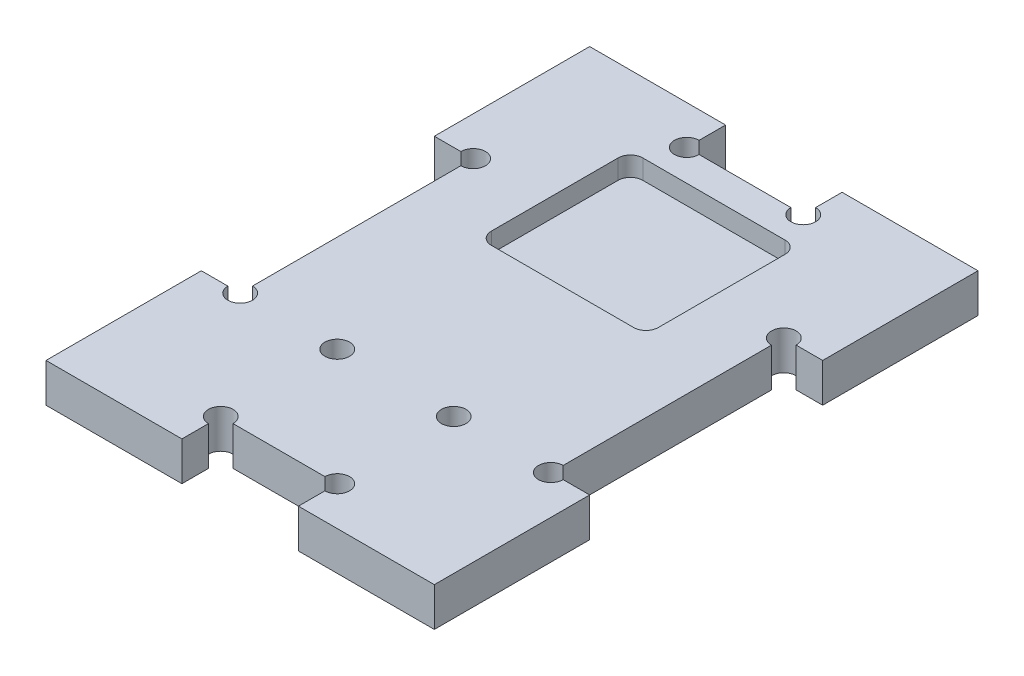
SolidWorks part; units mm, degrees
material "Acrylic (Medium-high impact)"
ref_plane "Front Plane" through (0, 0, 0) normal (0, 0, 1) x (1, 0, 0)
ref_plane "Top Plane" through (0, 0, 0) normal (0, 1, 0) x (1, 0, 0)
ref_plane "Right Plane" through (0, 0, 0) normal (1, 0, 0) x (0, 0, -1)
sketch "Sketch1" plane through (0, 0, 0) normal (0, 1, 0) x (1, 0, 0)
  line L1 (0, 0) -> (50, 0)
  line L2 (0, 0) -> (0, 70)
  line L3 (0, 70) -> (50, 70)
  line L4 (50, 0) -> (50, 70)
  dimension "D1" = 70
  dimension "D2" = 50
extrude "Boss-Extrude1" add sketch "Sketch1" along normal blind 5
sketch "Sketch4" plane through (0, 0, 0) normal (0, -1, 0) x (1, 0, 0)
  line L0 (25, 0) -> (25, -70) construction
  line L1 (34.1625, -61) -> (15.8375, -61)
  line L2 (35.75, -59.4125) -> (35.75, -43.0875)
  line L3 (34.1625, -41.5) -> (15.8375, -41.5)
  line L4 (14.25, -59.4125) -> (14.25, -43.0875)
  line L5 (35.75, -61) -> (14.25, -41.5) construction
  line L6 (35.75, -41.5) -> (14.25, -61) construction
  line L7 (50, -70) -> (0, -70) construction
  line L8 (0, 0) -> (50, 0) construction
  arc A0 (15.8375, -61) -> (14.25, -59.4125) centre (15.8375, -59.4125) cw
  arc A1 (34.1625, -61) -> (35.75, -59.4125) centre (34.1625, -59.4125) ccw
  arc A2 (35.75, -43.0875) -> (34.1625, -41.5) centre (34.1625, -43.0875) ccw
  arc A3 (15.8375, -41.5) -> (14.25, -43.0875) centre (15.8375, -43.0875) ccw
  point P0 (25, -51.25)
  dimension "D3" = 1.5875
  dimension "D1" = 19.5
  dimension "D2" = 21.5
  dimension "D4" = 9
extrude "Cut-Extrude2" cut sketch "Sketch4" along direction (0, -1, 0) on the side against the normal blind 2.5 from offset 2.5 offset against normal yes
sketch "Sketch5" plane through (0, 5, 0) normal (0, 1, 0) x (1, 0, 0)
  line L0 (0, 70) -> (0, 0) construction
  line L1 (0, 20) -> (5, 20)
  line L2 (0, 20) -> (0, 50)
  line L3 (0, 50) -> (5, 50)
  line L4 (5, 20) -> (5, 50)
  line L5 (50, 70) -> (0, 70) construction
  line L6 (32.5, 70) -> (17.5, 70)
  line L7 (32.5, 70) -> (32.5, 65)
  line L8 (32.5, 65) -> (17.5, 65)
  line L9 (17.5, 70) -> (17.5, 65)
  line L10 (50, 0) -> (50, 70) construction
  line L11 (50, 50) -> (45, 50)
  line L12 (50, 50) -> (50, 20)
  line L13 (50, 20) -> (45, 20)
  line L14 (45, 50) -> (45, 20)
  line L15 (0, 0) -> (50, 0) construction
  line L16 (17.5, 0) -> (32.5, 0)
  line L17 (17.5, 0) -> (17.5, 5)
  line L18 (17.5, 5) -> (32.5, 5)
  line L19 (32.5, 0) -> (32.5, 5)
  point P25 (0, 35)
  point P26 (25, 0)
  dimension "D1" = 5
  dimension "D2" = 30
  dimension "D3" = 15
extrude "Cut-Extrude3" cut sketch "Sketch5" against normal through all both and the other way through all
sketch "Sketch6" plane through (0, 5, 0) normal (0, 1, 0) x (1, 0, 0)
  line L0 (17.5, 5) -> (32.5, 5) construction
  line L1 (5, 20) -> (45, 20) construction
  line L2 (17.5, 5) -> (17.5, 20) construction
  line L3 (32.5, 5) -> (32.5, 20) construction
  circle A0 centre (5, 20) radius 1.5875
  circle A1 centre (5, 50) radius 1.5875
  circle A2 centre (17.5, 65) radius 1.5875
  circle A3 centre (32.5, 65) radius 1.5875
  circle A4 centre (45, 50) radius 1.5875
  circle A5 centre (45, 20) radius 1.5875
  circle A6 centre (32.5, 5) radius 1.5875
  circle A7 centre (17.5, 5) radius 1.5875
  circle A8 centre (17.5, 20) radius 1.5875
  circle A9 centre (32.5, 20) radius 1.5875
  dimension "D1" = 3.175
extrude "Cut-Extrude4" cut sketch "Sketch6" against normal through all
equation "\"cortador\"=3.175"
equation "\"D1@Sketch6\"=\"cortador\""
equation "\"D3@Sketch4\"=\"cortador\"/2"
